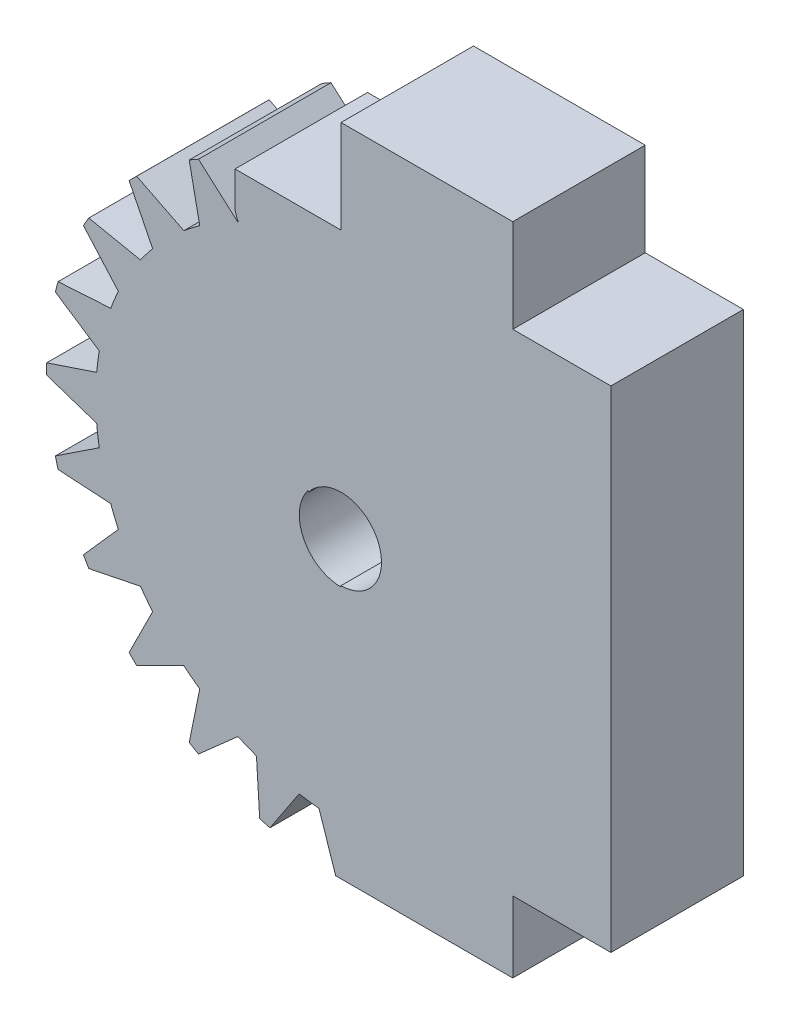
SolidWorks part; units mm, degrees
ref_plane "Front Plane" through (0, 0, 0) normal (0, 0, 1) x (1, 0, 0)
ref_plane "Top Plane" through (0, 0, 0) normal (0, 1, 0) x (1, 0, 0)
ref_plane "Right Plane" through (0, 0, 0) normal (1, 0, 0) x (0, 0, -1)
sketch "Sketch1" plane through (0, 0, 0) normal (0, 0, 1) x (1, 0, 0)
  circle A0 centre (0, 0) radius 10
  dimension "D1" = 20
extrude "Boss-Extrude1" add sketch "Sketch1" along normal blind 5.4
sketch "Sketch2" plane through (0, 0, 0) normal (0, 0, 1) x (1, 0, 0)
  line L2 (0, 12.65) -> (-0.9, 9.9594)
  line L3 (0, 12.65) -> (0.9, 9.9594)
  arc A0 (0.9, 9.9594) -> (-0.9, 9.9594) centre (0, 0) ccw
  dimension "D1" = 20
  dimension "D3" = 2.8371
  dimension "D4" = 1.8
extrude "Boss-Extrude2" add sketch "Sketch2" along normal blind 5.4
pattern_circular "CirPattern1" count 24 every 15 about axis through (0, 0, 0) along (0, 0, 1) of "Boss-Extrude2"
sketch "Sketch3" plane through (0, 0, 0) normal (0, 0, 1) x (1, 0, 0)
  circle A0 centre (0, 0) radius 12
  circle A1 centre (0, 0) radius 12.65
  dimension "D1" = 24
  dimension "D2" = 25.3
extrude "Cut-Extrude1" cut sketch "Sketch3" along normal blind 6
sketch "Sketch4" plane through (0, 0, 0) normal (0, 0, 1) x (1, 0, 0)
  line L0 (0, 0) -> (0, -12)
  line L1 (0, 0) -> (-20.8486, 0) construction
  line L2 (0, 0) -> (-3.8268, -9.2388) construction
  line L3 (-3.8268, 9.2388) -> (-4.5922, 11.0866)
  line L4 (-3.8268, -9.2388) -> (-4.5922, -11.0866) construction
  line L5 (0, 0) -> (-3.8268, 9.2388)
  arc A0 (0, -12) -> (-4.5922, 11.0866) centre (0, 0) ccw
  arc A2 (-4.2003, -9.0751) -> (-3.447, -9.3871) centre (0, 0) ccw construction
  dimension "D1" = 22.5
extrude "Cut-Extrude2" cut sketch "Sketch4" along normal blind 6
sketch "Sketch5" plane through (0, 0, 0) normal (0, 0, 1) x (1, 0, 0)
  circle A0 centre (0, 0) radius 1.7
  dimension "D1" = 3.4
extrude "Cut-Extrude3" cut sketch "Sketch5" along normal blind 6
sketch "Sketch6" plane through (0, 0, 0) normal (0, 0, 1) x (1, 0, 0)
  line L0 (0, 65.7933) -> (0, 76.1433) construction
  line L1 (-40.712, 32.0716) -> (40.712, 32.0716) construction
  line L2 (-4.32, 9.4388) -> (-4.32, 10.9)
  line L3 (11, 73.2433) -> (7, 73.2433) construction
  line L4 (-1.3286, 0.9785) -> (-4.32, 9.4388)
  line L5 (7, 73.2433) -> (7, 76.1433) construction
  line L6 (11, 53.2433) -> (11, 73.2433) construction
  line L7 (11, 53.2433) -> (7, 53.2433) construction
  line L8 (7, 53.2433) -> (7, 49.4433) construction
  line L9 (0, 10.9) -> (0, 14.7)
  line L10 (0, 76.1433) -> (7, 76.1433) construction
  line L11 (-4.32, 10.9) -> (0, 10.9)
  line L12 (7, 14.7) -> (0, 14.7)
  line L13 (0, -12) -> (7, -12)
  line L14 (7, 49.4433) -> (0, 49.4433) construction
  line L15 (-4.32, 53.2433) -> (0, 53.2433) construction
  line L16 (0, 53.2433) -> (0, 49.4433) construction
  line L17 (-1.3286, 63.1648) -> (-4.32, 54.7045) construction
  line L18 (-4.32, 54.7045) -> (-4.32, 53.2433) construction
  line L19 (7, 10.9) -> (7, 14.7)
  line L20 (11, 10.9) -> (7, 10.9)
  line L21 (11, 10.9) -> (11, -9.1)
  line L22 (7, -9.1) -> (7, -12)
  line L23 (11, -9.1) -> (7, -9.1)
  line L24 (0, -1.65) -> (0, -12)
  line L25 (0, 64.1433) -> (0, 0) construction
  arc A0 (-1.3286, 63.1648) -> (0, 65.7933) centre (0, 64.1433) ccw construction
  arc A1 (-1.3286, 0.9785) -> (0, -1.65) centre (0, 0) cw
  dimension "D2" = 2.9
  dimension "D6" = 7
  dimension "D3" = 1.65
  dimension "D4" = 20
  dimension "D5" = 4
  dimension "D7" = 3.8
  dimension "D8" = 7
  dimension "D9" = 4.32
  dimension "D11" = 4
extrude "Boss-Extrude3" add sketch "Sketch6" along normal blind 5.4
sketch "Sketch7" [suppressed] plane through (0, 0, 6) normal (0, 0, 1) x (1, 0, 0)
  line L0 (-0.2181, 11.998) -> (7, 12)
  line L1 (7, 12) -> (7, 9.9045)
  line L2 (7, 9.9045) -> (11, 9.9045)
  line L3 (11, 9.9045) -> (11, -10.0955)
  line L4 (11, -10.0955) -> (7, -10.0955)
  line L5 (7, -10.0955) -> (7, -13.0955)
  line L6 (7, -13.0955) -> (0, -13.0955)
  line L7 (0, -13.0955) -> (0, -10.0955)
  line L8 (0, -10.0955) -> (-3.8268, -10.0955)
  line L9 (-3.8268, -10.0955) -> (-3.8268, -9.2388)
  line L10 (-0.2181, 11.998) -> (-0.9, 9.9594)
  line L11 (-1.7084, 9.853) -> (-2.8947, 11.6456)
  line L12 (-2.8947, 11.6456) -> (-3.316, 11.5328)
  line L13 (-3.316, 11.5328) -> (-3.447, 9.3871)
  line L14 (-4.2003, 9.0751) -> (-5.8101, 10.4996)
  line L15 (-5.8101, 10.4996) -> (-6.1879, 10.2815)
  line L16 (-6.1879, 10.2815) -> (-5.7591, 8.1751)
  line L17 (-6.406, 7.6788) -> (-8.3297, 8.6381)
  line L18 (-8.3297, 8.6381) -> (-8.6381, 8.3297)
  line L19 (-8.6381, 8.3297) -> (-7.6788, 6.406)
  line L20 (-8.1751, 5.7591) -> (-10.2815, 6.1879)
  line L21 (-10.2815, 6.1879) -> (-10.4996, 5.8101)
  line L22 (-10.4996, 5.8101) -> (-9.0751, 4.2003)
  line L23 (-9.3871, 3.447) -> (-11.5328, 3.316)
  line L24 (-11.5328, 3.316) -> (-11.6456, 2.8947)
  line L25 (-11.6456, 2.8947) -> (-9.853, 1.7084)
  line L26 (-9.9594, 0.9) -> (-11.998, 0.2181)
  line L27 (-11.998, 0.2181) -> (-11.998, -0.2181)
  line L28 (-11.998, -0.2181) -> (-9.9594, -0.9)
  line L29 (-9.853, -1.7084) -> (-11.6456, -2.8947)
  line L30 (-11.6456, -2.8947) -> (-11.5328, -3.316)
  line L31 (-11.5328, -3.316) -> (-9.3871, -3.447)
  line L32 (-9.0751, -4.2003) -> (-10.4996, -5.8101)
  line L33 (-10.4996, -5.8101) -> (-10.2815, -6.1879)
  line L34 (-10.2815, -6.1879) -> (-8.1751, -5.7591)
  line L35 (-7.6788, -6.406) -> (-8.6381, -8.3297)
  line L36 (-7.6788, -6.406) -> (-8.6381, -8.3297) construction
  line L37 (-8.6381, -8.3297) -> (-8.3297, -8.6381)
  line L38 (-8.3297, -8.6381) -> (-6.406, -7.6788)
  line L39 (-5.7591, -8.1751) -> (-6.1879, -10.2815)
  line L40 (-6.1879, -10.2815) -> (-5.8101, -10.4996)
  line L41 (-5.8101, -10.4996) -> (-4.2003, -9.0751)
  circle A0 centre (0, 0) radius 1.5
  arc A1 (-0.9, 9.9594) -> (-1.7084, 9.853) centre (0, 0) ccw
  arc A2 (-3.447, 9.3871) -> (-4.2003, 9.0751) centre (0, 0) ccw
  arc A3 (-5.7591, 8.1751) -> (-6.406, 7.6788) centre (0, 0) ccw
  arc A4 (-7.6788, 6.406) -> (-8.1751, 5.7591) centre (0, 0) ccw
  arc A5 (-9.0751, 4.2003) -> (-9.3871, 3.447) centre (0, 0) ccw
  arc A6 (-9.853, 1.7084) -> (-9.9594, 0.9) centre (0, 0) ccw
  arc A7 (-4.2003, -9.0751) -> (-3.8268, -9.2388) centre (0, 0) ccw
  arc A8 (-6.406, -7.6788) -> (-5.7591, -8.1751) centre (0, 0) ccw
  arc A9 (-8.1751, -5.7591) -> (-7.6788, -6.406) centre (0, 0) ccw
  arc A10 (-9.3871, -3.447) -> (-9.0751, -4.2003) centre (0, 0) ccw
  arc A11 (-9.9594, -0.9) -> (-9.853, -1.7084) centre (0, 0) ccw
equation "\"D2@Sketch6\"= 2.1 + \"tol2@parametersSketch@prostheticParameters.SLDPRT\" * 2"
equation "\"D7@Sketch6\"= 3 + \"tol2@parametersSketch@prostheticParameters.SLDPRT\" * 2"
equation "\"D1@Boss-Extrude3\" = 5.8 - \"tol2@parametersSketch@prostheticParameters.SLDPRT\""
equation "\"D1@Boss-Extrude1\" = 5.8 - \"tol2@parametersSketch@prostheticParameters.SLDPRT\""
equation "\"D1@Boss-Extrude2\"= 5.8 - \"tol2@parametersSketch@prostheticParameters.SLDPRT\""
equation "\"D1@Sketch5\"= 3 + \"tol1@parametersSketch@prostheticParameters.SLDPRT\""
